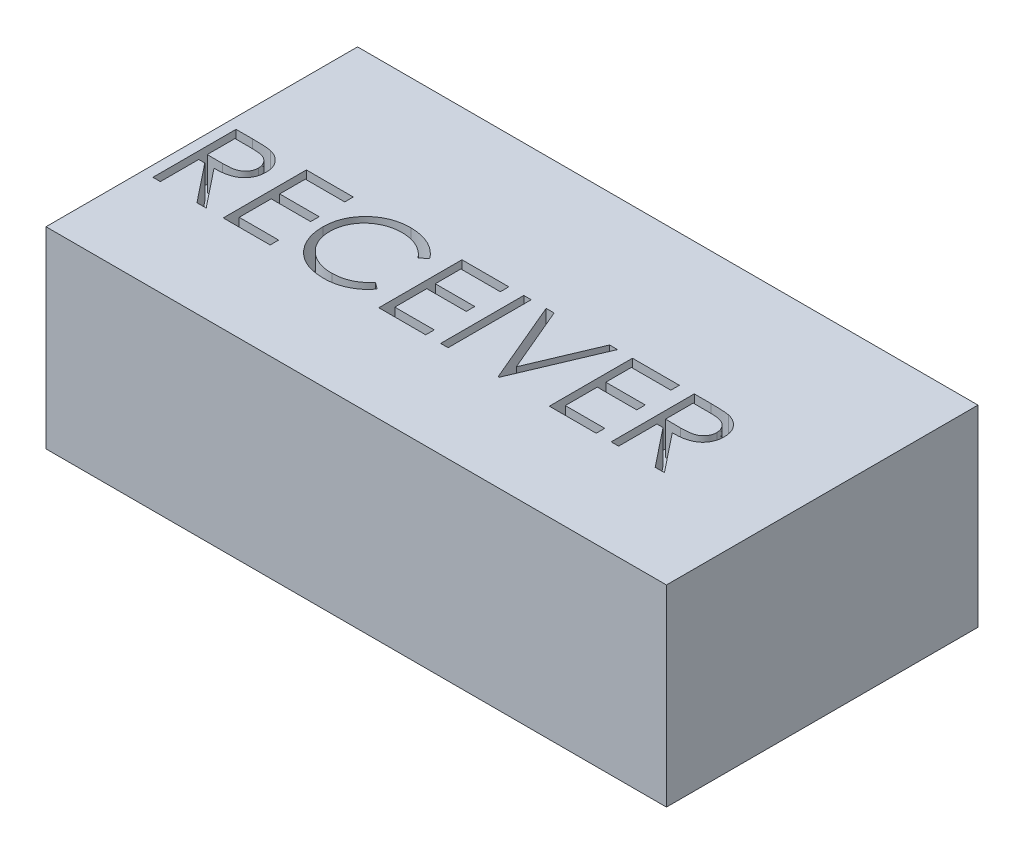
SolidWorks part; units mm, degrees
ref_plane "Front Plane" through (0, 0, 0) normal (0, 0, 1) x (1, 0, 0)
ref_plane "Top Plane" through (0, 0, 0) normal (0, 1, 0) x (1, 0, 0)
ref_plane "Right Plane" through (0, 0, 0) normal (1, 0, 0) x (0, 0, -1)
sketch "Sketch1" plane through (0, 0, 0) normal (0, 1, 0) x (1, 0, 0)
  line L1 (-23.7, 11.9) -> (23.7, 11.9)
  line L2 (-23.7, 11.9) -> (-23.7, -11.9)
  line L3 (-23.7, -11.9) -> (23.7, -11.9)
  line L4 (23.7, 11.9) -> (23.7, -11.9)
  line L5 (-23.7, 11.9) -> (23.7, -11.9) construction
  line L6 (-23.7, -11.9) -> (23.7, 11.9) construction
  point P0 (0, 0)
  dimension "D1" = 47.4
  dimension "D2" = 23.8
extrude "Boss-Extrude1" add sketch "Sketch1" along normal blind 14.7
sketch "Sketch2" plane through (0, 14.7, 0) normal (0, 1, 0) x (1, 0, 0)
  line L0 (-23.7, -4.5469) -> (23.7, -4.5469) construction
  line L1 (-23.7, 11.9) -> (-23.7, -11.9) construction
  line L2 (23.7, -11.9) -> (23.7, 11.9) construction
  text T0 "RECEIVER" font "Century Gothic" height in points 24
extrude "Cut-Extrude1" cut sketch "Sketch2" against normal blind 2.54
